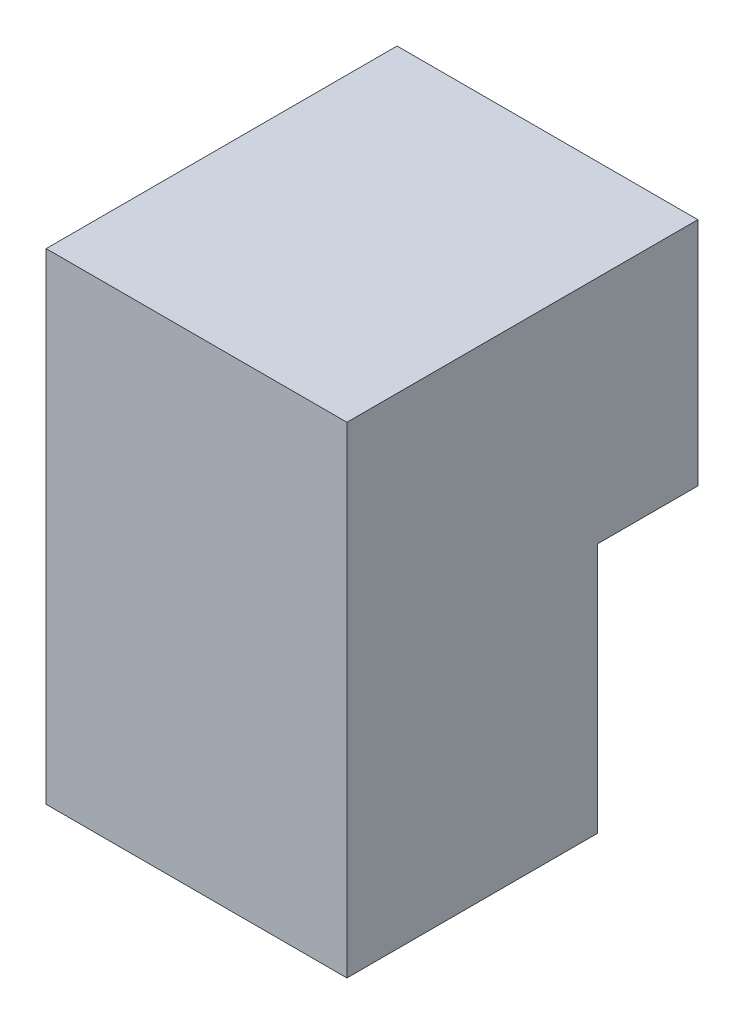
SolidWorks part; units mm, degrees
ref_plane "Front Plane" through (0, 0, 0) normal (1, 0, 0) x (0, 1, 0)
ref_plane "Top Plane" through (0, 0, 0) normal (0, 0, 1) x (0, 1, 0)
ref_plane "Right Plane" through (0, 0, 0) normal (0, 1, 0) x (-1, 0, 0)
sketch "Sketch1" plane through (0, 0, 0) normal (1, 0, 0) x (0, 1, 0)
  line L1 (-24, -17.5) -> (24, -17.5)
  line L2 (-24, -17.5) -> (-24, 17.5)
  line L3 (-24, 17.5) -> (24, 17.5)
  line L4 (24, -17.5) -> (24, 17.5)
  line L5 (-24, -17.5) -> (24, 17.5) construction
  line L6 (-24, 17.5) -> (24, -17.5) construction
  line L11 (-24, -17.5) -> (1, -17.5)
  line L12 (-24, -17.5) -> (-24, -7.5)
  line L13 (-24, -7.5) -> (1, -7.5)
  line L14 (1, -17.5) -> (1, -7.5)
  point P0 (0, 0)
  dimension "D1" = 48
  dimension "D2" = 35
  dimension "D3" = 25
  dimension "D4" = 10
extrude "Boss-Extrude1" add sketch "Sketch1" along normal blind 30 contours L14 L1 L4 L3 L2 L13
